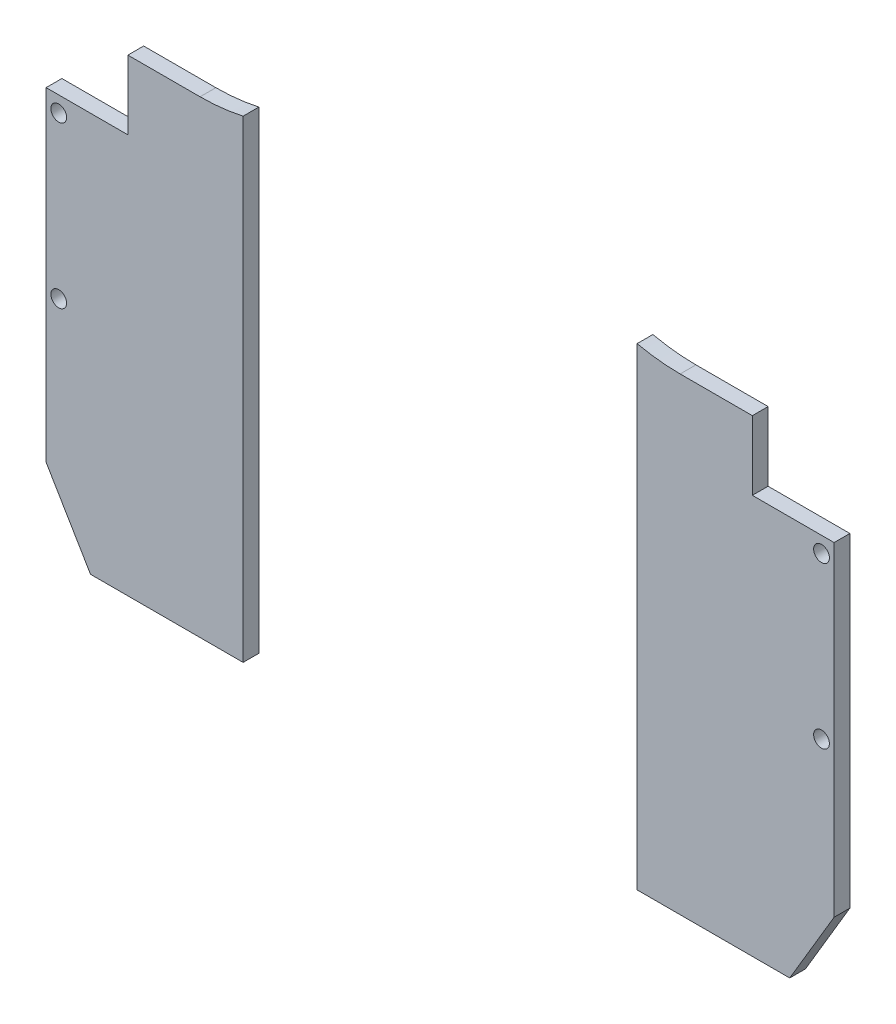
SolidWorks part; units mm, degrees
ref_plane "Front Plane" through (0, 0, 0) normal (0, 0, 1) x (1, 0, 0)
ref_plane "Top Plane" through (0, 0, 0) normal (0, 1, 0) x (1, 0, 0)
ref_plane "Right Plane" through (0, 0, 0) normal (1, 0, 0) x (0, 0, -1)
sketch "Sketch1" plane through (0, 0, 0) normal (0, 0, 1) x (1, 0, 0)
  line L62 (-3368.0419, -66.9192) -> (-3368.0419, -288.0048) construction
  line L68 (-3493.0419, -66.9192) -> (-3243.0419, -66.9192)
  line L78 (-3493.0419, -66.9192) -> (-3493.0419, -288.0048)
  line L79 (-3243.0419, -66.9192) -> (-3243.0419, -288.0048)
  line L80 (-3493.0419, -288.0048) -> (-3243.0419, -288.0048)
  line L83 (-3493.0419, -161.3192) -> (-3493.0419, -259.0407) construction
  line L87 (-3353.5801, -66.9192) -> (-3382.5038, -66.9192) construction
  line L90 (-3243.0419, -259.0407) -> (-3243.0419, -161.3192) construction
  circle A6 centre (-3489.0419, -217.3192) radius 2.5
  circle A7 centre (-3489.0419, -166.3192) radius 2.5
  circle A14 centre (-3489.0419, -217.3192) radius 2.1 construction
  circle A15 centre (-3489.0419, -166.3192) radius 2.5 construction
  circle A16 centre (-3489.0419, -217.3192) radius 2.5 construction
  circle A17 centre (-3247.0419, -166.3192) radius 2.5
  circle A18 centre (-3247.0419, -217.3192) radius 2.5
extrude "Boss-Extrude1" add sketch "Sketch1" along normal blind 5
ref_plane "Plane1"
sketch "Sketch6" plane through (0, 0, 0) normal (0, 0, 1) x (1, 0, 0)
  line L13 (-3503.4579, -270.4515) -> (-3493.0419, -264.2708)
  line L19 (-3493.0419, -161.3192) -> (-3493.0419, -66.9192)
  line L25 (-3503.4579, -270.4515) -> (-3489.3744, -294.1855)
  line L29 (-3493.0419, -161.3192) -> (-3467.1019, -161.3192)
  line L30 (-3493.0419, -66.9192) -> (-3382.5038, -66.9192)
  line L31 (-3467.1019, -161.3192) -> (-3467.1019, -139.4192)
  line L33 (-3493.0419, -264.2708) -> (-3478.9585, -288.0048)
  line L37 (-3493.0419, -161.3192) -> (-3467.1019, -161.3192) construction
  line L38 (-3353.5801, -66.9192) -> (-3382.5038, -66.9192) construction
  line L40 (-3467.1019, -161.3192) -> (-3467.1019, -139.4192) construction
  line L41 (-3493.0419, -161.3192) -> (-3493.0419, -259.0407) construction
  line L43 (-3467.1019, -139.4192) -> (-3444.1986, -139.4192)
  line L44 (-3467.1019, -139.4192) -> (-3445.0038, -139.4192) construction
  line L45 (-3489.3744, -294.1855) -> (-3478.9585, -288.0048)
  line L47 (-3493.0419, -66.9192) -> (-3493.0419, -288.0048) construction
  line L48 (-3493.0419, -288.0048) -> (-3243.0419, -288.0048) construction
  line L49 (-3368.0419, -66.9192) -> (-3368.0419, -288.0048) construction
  line L50 (-3243.0419, -66.9192) -> (-3493.0419, -66.9192) construction
  line L51 (-3246.7095, -294.1855) -> (-3257.1254, -288.0048)
  line L52 (-3268.9819, -139.4192) -> (-3291.8853, -139.4192)
  line L53 (-3243.0419, -264.2708) -> (-3257.1254, -288.0048)
  line L54 (-3268.9819, -161.3192) -> (-3268.9819, -139.4192)
  line L55 (-3243.0419, -66.9192) -> (-3353.5801, -66.9192)
  line L56 (-3243.0419, -161.3192) -> (-3268.9819, -161.3192)
  line L57 (-3232.626, -270.4515) -> (-3246.7095, -294.1855)
  line L58 (-3243.0419, -161.3192) -> (-3243.0419, -66.9192)
  line L59 (-3232.626, -270.4515) -> (-3243.0419, -264.2708)
  arc A1 (-3444.1986, -139.4192) -> (-3382.5038, -66.9192) centre (-3444.1986, -76.9192) ccw
  arc A2 (-3291.8853, -139.4192) -> (-3353.5801, -66.9192) centre (-3291.8853, -76.9192) cw
  circle A3 centre (-3368.0419, -300.4173) radius 62.5
  arc A4 (-3305.5419, -300.4173) -> (-3430.5419, -300.4173) centre (-3368.0419, -300.4173) ccw construction
  dimension "D1" = 62.5
extrude "Cut-Extrude4" cut sketch "Sketch6" along normal through all
sketch "Sketch7" plane through (0, 0, 5) normal (0, 0, 1) x (1, 0, 0)
  line L4 (-3493.0419, -161.3192) -> (-3493.0419, -264.2708) construction
  line L6 (-3430.5419, -66.9192) -> (-3430.5419, -365.6173)
  line L7 (-3305.5419, -66.9192) -> (-3305.5419, -365.6173)
  line L8 (-3430.5419, -365.6173) -> (-3305.5419, -365.6173)
  line L9 (-3243.0419, -264.2708) -> (-3243.0419, -161.3192) construction
  line L10 (-3430.5419, -66.9192) -> (-3305.5419, -66.9192)
  line L11 (-3353.5801, -66.9192) -> (-3382.5038, -66.9192) construction
  line L12 (-3430.5419, -66.9192) -> (-3430.5419, -365.6173) construction
  line L15 (-3305.5419, -66.9192) -> (-3305.5419, -365.6173) construction
  line L16 (-3310.5419, -365.6173) -> (-3425.5419, -365.6173) construction
  circle A4 centre (-3368.0419, -175.4173) radius 62.5 construction
  circle A6 centre (-3368.0419, -175.4173) radius 62.5 construction
extrude "Cut-Extrude5" cut sketch "Sketch7" against normal blind 5
